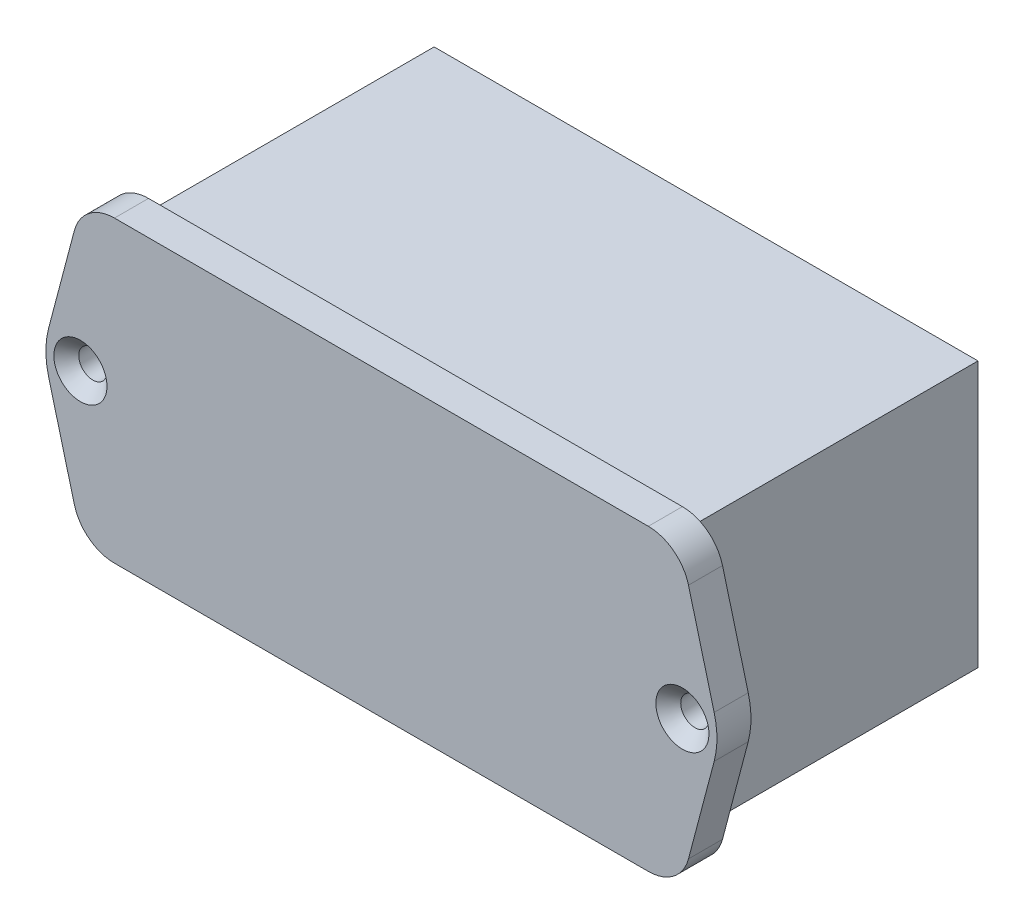
SolidWorks part; units mm, degrees
ref_plane "Piano frontale" through (0, 0, 0) normal (0, 0, 1) x (1, 0, 0)
ref_plane "Piano superiore" through (0, 0, 0) normal (0, 1, 0) x (1, 0, 0)
ref_plane "Piano destro" through (0, 0, 0) normal (1, 0, 0) x (0, 0, -1)
sketch "Schizzo1" plane through (0, 0, 0) normal (0, 0, 1) x (1, 0, 0)
  line L0 (0, 0) -> (0, 60.2364) construction
  line L1 (0, 0) -> (-72.5, 0) construction
  line L2 (32.1483, 18) -> (-32.1483, 18)
  line L3 (-36.9828, 14.2758) -> (-40.0767, 2.5515)
  line L4 (36.9828, 14.2758) -> (40.0767, 2.5515)
  line L5 (36.9828, -14.2758) -> (40.0767, -2.5515)
  line L6 (-36.9828, -14.2758) -> (-40.0767, -2.5515)
  line L7 (32.1483, -18) -> (-32.1483, -18)
  arc A0 (-36.9828, 14.2758) -> (-32.1483, 18) centre (-32.1483, 13) cw
  circle A1 centre (-36.25, 0) radius 1.7
  arc A2 (36.9828, 14.2758) -> (32.1483, 18) centre (32.1483, 13) ccw
  arc A3 (36.9828, -14.2758) -> (32.1483, -18) centre (32.1483, -13) cw
  arc A4 (-36.9828, -14.2758) -> (-32.1483, -18) centre (-32.1483, -13) ccw
  circle A5 centre (36.25, 0) radius 1.7
  arc A6 (40.0767, -2.5515) -> (40.0767, 2.5515) centre (30.4077, 0) ccw
  arc A7 (-40.0767, -2.5515) -> (-40.0767, 2.5515) centre (-30.4077, 0) cw
  point P9 (-36, 18)
  point P16 (0, 18)
  point P22 (0, -18)
  point P23 (-36, -18)
  point P28 (40.75, 0)
  point P31 (-40.75, 0)
  dimension "D4" = 5
  dimension "D6" = 3.4
  dimension "D7" = 10
  dimension "D8" = 10
  dimension "D1" = 18
  dimension "D2" = 40.75
  dimension "D3" = 36
  dimension "D5" = 36.25
extrude "Estrusione-Estrusione1" add sketch "Schizzo1" against normal blind 4.1
sketch "Schizzo2" plane through (0, 0, -4.1) normal (0, 0, -1) x (-1, 0, 0)
  line L1 (32.75, -16) -> (-32.75, -16)
  line L2 (32.75, -16) -> (32.75, 16)
  line L3 (32.75, 16) -> (-32.75, 16)
  line L4 (-32.75, -16) -> (-32.75, 16)
  line L5 (32.75, -16) -> (-32.75, 16) construction
  line L6 (32.75, 16) -> (-32.75, -16) construction
  point P0 (0, 0)
  dimension "D1" = 65.5
  dimension "D2" = 32
extrude "Estrusione-Sottile1" add sketch "Schizzo2" along normal blind 35 thin
chamfer "Smusso1" distance 1.5 angle 45 2 edges at (34.55, 0, 0) (-34.55, 0, 0)
